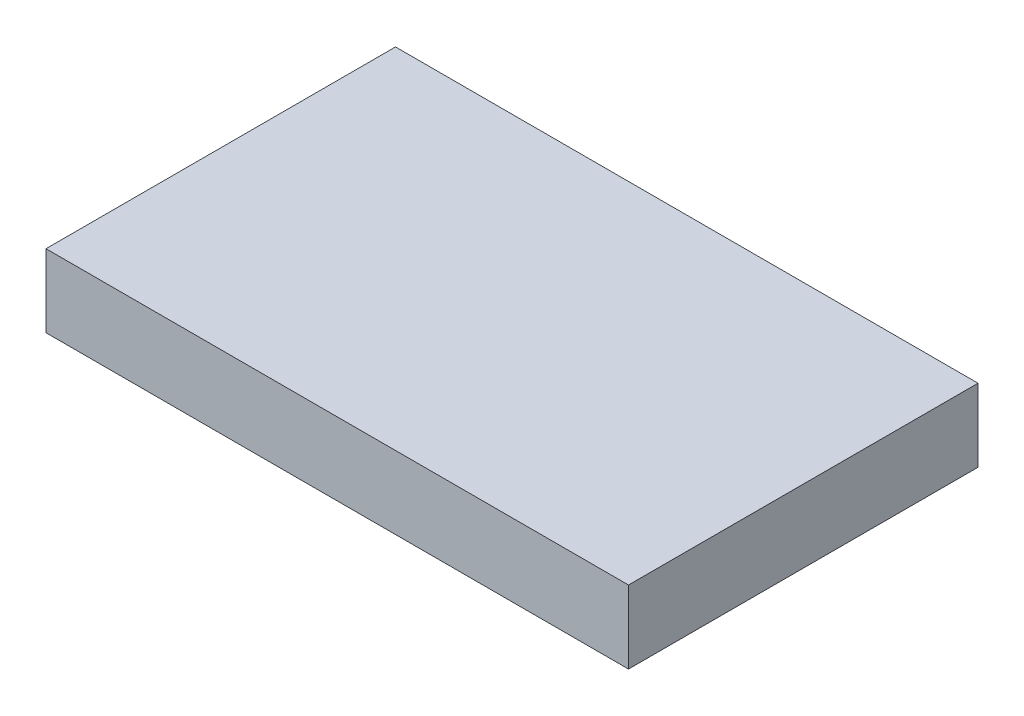
SolidWorks part; units mm, degrees
other "Markup1"
sketch "Sketch2" plane through (25.4, 3.175, 15.24) normal (0.1258, 0.5812, 0.804) x (0.9459, 0.1741, -0.2739)
ref_plane "Front Plane" through (0, 0, 0) normal (0, 0, 1) x (1, 0, 0)
ref_plane "Top Plane" through (0, 0, 0) normal (0, 1, 0) x (1, 0, 0)
ref_plane "Right Plane" through (0, 0, 0) normal (1, 0, 0) x (0, 0, -1)
sketch "Sketch1" plane through (0, 0, 0) normal (0, 1, 0) x (1, 0, 0)
  line L1 (-25.4, -15.24) -> (25.4, -15.24)
  line L2 (-25.4, -15.24) -> (-25.4, 15.24)
  line L3 (-25.4, 15.24) -> (25.4, 15.24)
  line L4 (25.4, -15.24) -> (25.4, 15.24)
  line L5 (-25.4, -15.24) -> (25.4, 15.24) construction
  line L6 (-25.4, 15.24) -> (25.4, -15.24) construction
  point P0 (0, 0)
  dimension "D1" = 50.8
  dimension "D2" = 30.48
extrude "Boss-Extrude1" add sketch "Sketch1" along normal mid plane 6.35
